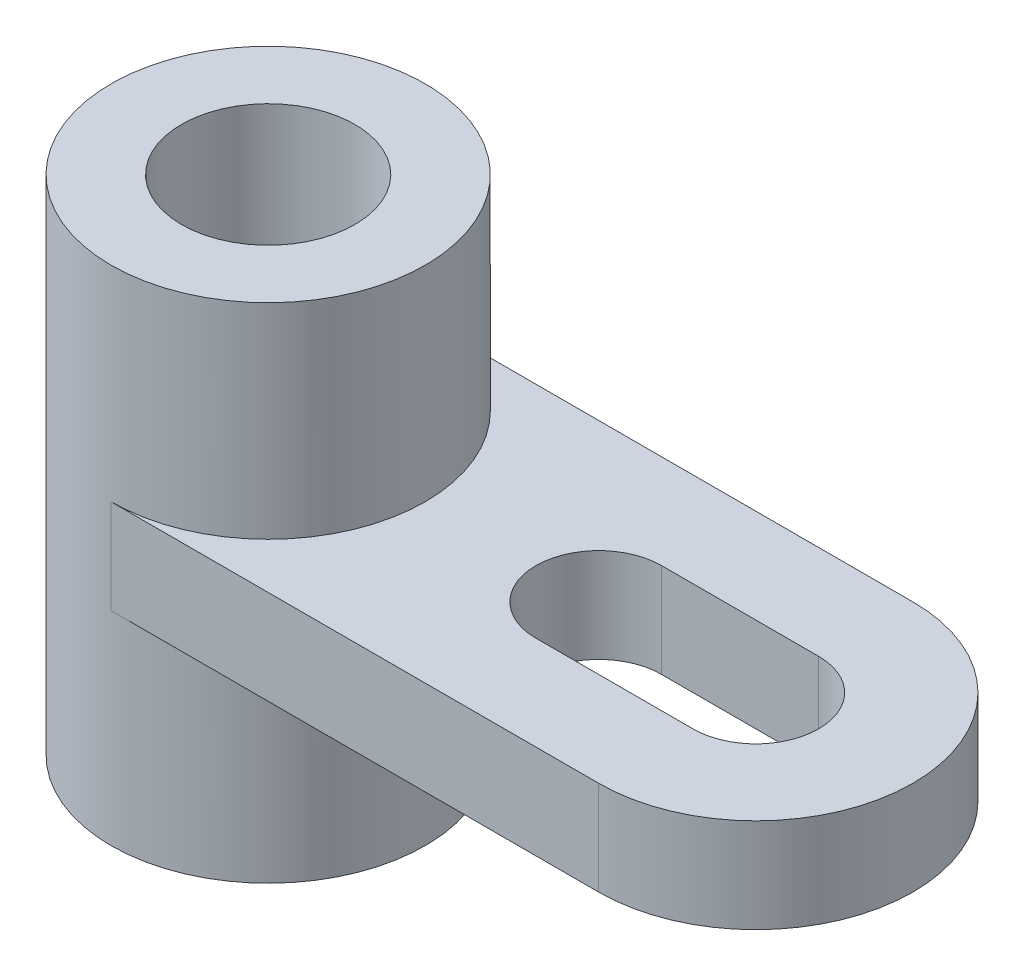
SolidWorks part; units mm, degrees
ref_plane "Front Plane" through (0, 0, 0) normal (0, 0, 1) x (1, 0, 0)
ref_plane "Top Plane" through (0, 0, 0) normal (0, 1, 0) x (1, 0, 0)
ref_plane "Right Plane" through (0, 0, 0) normal (1, 0, 0) x (0, 0, -1)
sketch "Sketch1" plane through (0, 0, 0) normal (0, 1, 0) x (1, 0, 0)
  line L1 (-49.276, 31.75) -> (49.276, 31.75)
  line L3 (-49.276, -31.75) -> (49.276, -31.75)
  arc A0 (-49.276, 31.75) -> (-49.276, -31.75) centre (-49.276, 0) ccw
  arc A1 (49.276, -31.75) -> (49.276, 31.75) centre (49.276, 0) ccw
  point P0 (0, 0)
  dimension "D1" = 98.552
  dimension "D2" = 63.5
extrude "Boss-Extrude1" add sketch "Sketch1" along normal blind 19.05
sketch "Sketch5" plane through (0, 0, 0) normal (0, -1, 0) x (1, 0, 0)
  line L0 (49.276, 31.75) -> (49.276, 12.7) construction
  line L1 (49.276, -12.7) -> (49.276, -31.75) construction
  line L2 (17.526, 12.7) -> (49.276, 12.7)
  line L4 (17.526, -12.7) -> (49.276, -12.7)
  arc A1 (17.526, 12.7) -> (17.526, -12.7) centre (17.526, 0) ccw
  arc A2 (49.276, -12.7) -> (49.276, 12.7) centre (49.276, 0) ccw
  point P4 (33.401, 0)
  dimension "D1" = 25.4
  dimension "D2" = 31.75
extrude "Cut-Extrude3" cut sketch "Sketch5" against normal through all
sketch "Sketch3" plane through (0, 19.05, 0) normal (0, 1, 0) x (1, 0, 0)
  line L0 (-49.276, 31.75) -> (-49.276, -31.75) construction
  circle A0 centre (-49.276, 0) radius 31.75
extrude "Boss-Extrude2" add sketch "Sketch3" along normal blind 41.402 and the other way blind 60.198
sketch "Sketch4" plane through (0, 60.452, 0) normal (0, 1, 0) x (1, 0, 0)
  line L0 (-49.276, 31.75) -> (-49.276, -31.75) construction
  circle A0 centre (-49.276, 0) radius 17.526
  dimension "D1" = 35.052
extrude "Cut-Extrude2" cut sketch "Sketch4" against normal through all
